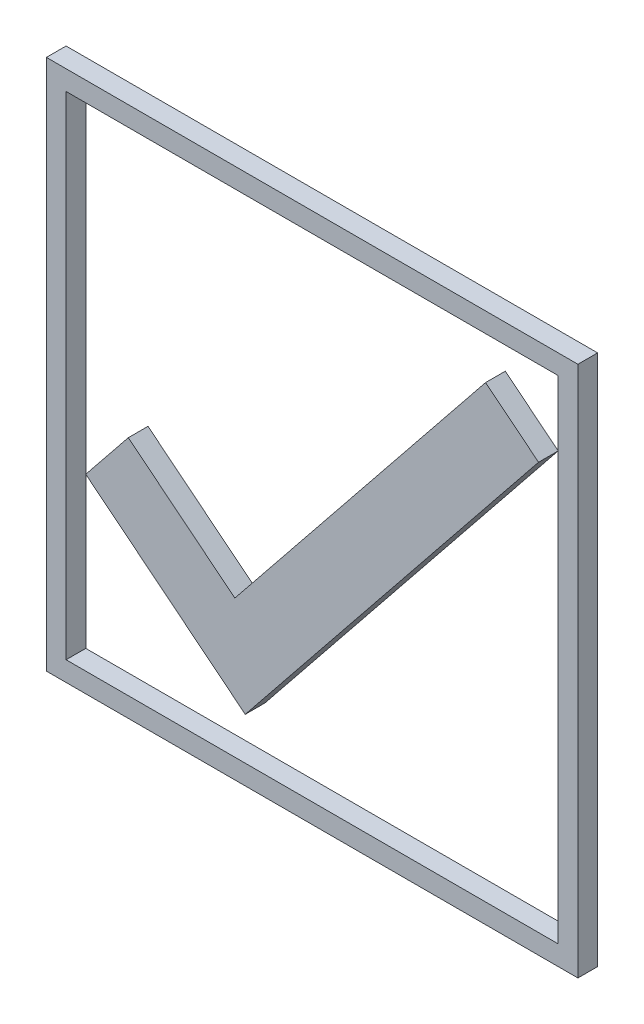
SolidWorks part; units mm, degrees
ref_plane "Ebene vorne" through (0, 0, 0) normal (0, 0, 1) x (1, 0, 0)
ref_plane "Ebene oben" through (0, 0, 0) normal (0, 1, 0) x (1, 0, 0)
ref_plane "Ebene rechts" through (0, 0, 0) normal (1, 0, 0) x (0, 0, -1)
sketch "Sketch1" plane through (0, 0, 0) normal (0, 0, 1) x (1, 0, 0)
  line L0 (-25, -25) -> (-25, 25)
  line L1 (-25, -25) -> (25, -25)
  line L2 (-25, 25) -> (25, 25)
  line L3 (25, -25) -> (25, 25)
  line L4 (-25, -25) -> (25, 25) construction
  line L5 (-25, 25) -> (25, -25) construction
  line L6 (-23, -7.6785) -> (-18.6777, -2.3)
  line L7 (-23, -23) -> (23, -23)
  line L8 (-23, -23) -> (-23, 23)
  line L9 (-23, 23) -> (23, 23)
  line L10 (23, -23) -> (23, 23)
  line L11 (-23, -23) -> (23, 23) construction
  line L12 (-23, 23) -> (23, -23) construction
  line L13 (-23, -7.6785) -> (-6.7964, -20.7)
  line L14 (-18.6777, -2.3) -> (-2.4742, -15.3215)
  line L15 (-6.7964, -20.7) -> (-2.4742, -15.3215)
  line L16 (-6.7964, -20.7) -> (23, 16.3777)
  line L17 (-6.7964, -20.7) -> (-12.1749, -16.3777)
  line L18 (23, 16.3777) -> (17.6215, 20.7)
  line L19 (-12.1749, -16.3777) -> (17.6215, 20.7)
  line L20 (-18.6777, -2.3) -> (-6.7964, -20.7) construction
  line L21 (-23, -7.6785) -> (-2.4742, -15.3215) construction
  line L22 (-6.7964, -20.7) -> (17.6215, 20.7) construction
  line L23 (-12.1749, -16.3777) -> (23, 16.3777) construction
  line L25 (-27, -27) -> (27, -27)
  line L26 (-27, -27) -> (-27, 27)
  line L27 (-27, 27) -> (27, 27)
  line L28 (27, -27) -> (27, 27)
  line L29 (-27, -27) -> (27, 27) construction
  line L30 (-27, 27) -> (27, -27) construction
  point P0 (0, 0)
  point P1 (0, 0)
  point P11 (0, 0)
  point P23 (-12.7371, -11.5)
  point P24 (5.4125, 0)
  point P27 (6.2051, -8.4517)
  point P28 (0.0031, -12.2389)
  dimension "D1" = 50
  dimension "D2" = 2
  dimension "D3" = 2.3
  dimension "D4" = 46
  dimension "D5" = 18.4
  dimension "D6" = 6.9
  dimension "D7" = 41.4
  dimension "D8" = 54
  dimension "D9" = 10.2629
  dimension "D10" = 11.5
  dimension "D11" = 17.5875
  dimension "D12" = 23
  dimension "D13" = 16.2036
extrude "Boss-Extrude1" add sketch "Sketch1" along normal blind 2 contours L19 L14 L16 L18 | L13 L19 L14 L6 | L19 L13 L15 L14 | L25 L28 L27 L26 L3 L1 L0 L2
